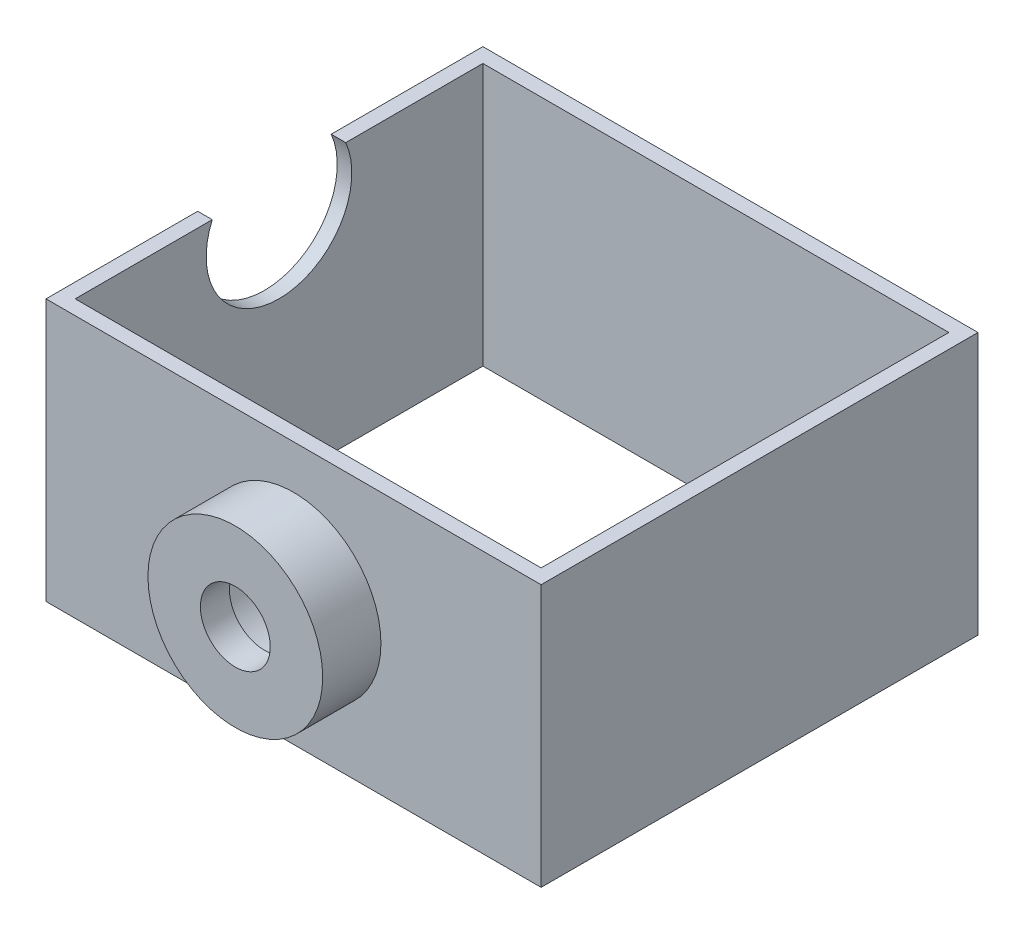
SolidWorks part; units mm, degrees
ref_plane "Front Plane" through (0, 0, 0) normal (0, 0, 1) x (1, 0, 0)
ref_plane "Top Plane" through (0, 0, 0) normal (0, 1, 0) x (1, 0, 0)
ref_plane "Right Plane" through (0, 0, 0) normal (1, 0, 0) x (0, 0, -1)
sketch "Sketch2" plane through (0, 0, 0) normal (0, 0, 1) x (1, 0, 0)
  circle A0 centre (0, 0) radius 15
  dimension "D1" = 30
extrude "Boss-Extrude1" add sketch "Sketch2" along normal blind 10
sketch "Sketch4" plane through (0, 0, 0) normal (0, 0, -1) x (-1, 0, 0)
  line L1 (-42.5, -22.5) -> (42.5, -22.5)
  line L2 (-42.5, -22.5) -> (-42.5, 22.5)
  line L3 (-42.5, 22.5) -> (42.5, 22.5)
  line L4 (42.5, -22.5) -> (42.5, 22.5)
  point P0 (0, 0)
  dimension "D1" = 85
  dimension "D2" = 45
  dimension "D3" = 22.5
  dimension "D4" = 42.5
extrude "Boss-Extrude2" add sketch "Sketch4" along normal blind 75
sketch "Sketch5" plane through (0, 22.5, 0) normal (0, 1, 0) x (1, 0, 0)
  line L0 (-42.5, 75) -> (-42.5, 0) construction
  line L5 (40, 2.5) -> (-40, 2.5)
  line L6 (40, 2.5) -> (40, 72.5)
  line L7 (40, 72.5) -> (-40, 72.5)
  line L8 (-40, 2.5) -> (-40, 72.5)
  line L9 (40, 2.5) -> (-40, 72.5) construction
  line L10 (40, 72.5) -> (-40, 2.5) construction
  line L11 (-42.5, 75) -> (42.5, 75) construction
  point P0 (0, 37.5)
  dimension "D1" = 80
  dimension "D2" = 2.5
  dimension "D3" = 2.5
  dimension "D4" = 70
extrude "Cut-Extrude3" cut sketch "Sketch5" against normal up to next
sketch "Sketch3" plane through (0, 0, 10) normal (0, 0, 1) x (1, 0, 0)
  circle A0 centre (0, 0) radius 6
  dimension "D1" = 12
extrude "Cut-Extrude1" cut sketch "Sketch3" against normal up to next
sketch "Sketch6" plane through (0, 0, -2.5) normal (0, 0, -1) x (-1, 0, 0)
  circle A0 centre (0, 0) radius 10
  dimension "D1" = 20
extrude "Cut-Extrude4" cut sketch "Sketch6" against normal blind 7.5
sketch "Sketch7" plane through (-42.5, 0, 0) normal (-1, 0, 0) x (0, 0, 1)
  line L1 (-75, 22.5) -> (0, 22.5) construction
  circle A0 centre (-37.5, 17.5) radius 12.5
  point P2 (-39.3205, 13.1785)
  point P3 (0, 0)
  point P4 (0, 0)
  point P5 (-37.5, 5.437)
  point P8 (0, 0)
  point P9 (-37.5, 22.5)
  dimension "D1" = 25
  dimension "D2" = 5
extrude "Cut-Extrude5" cut sketch "Sketch7" against normal up to next
